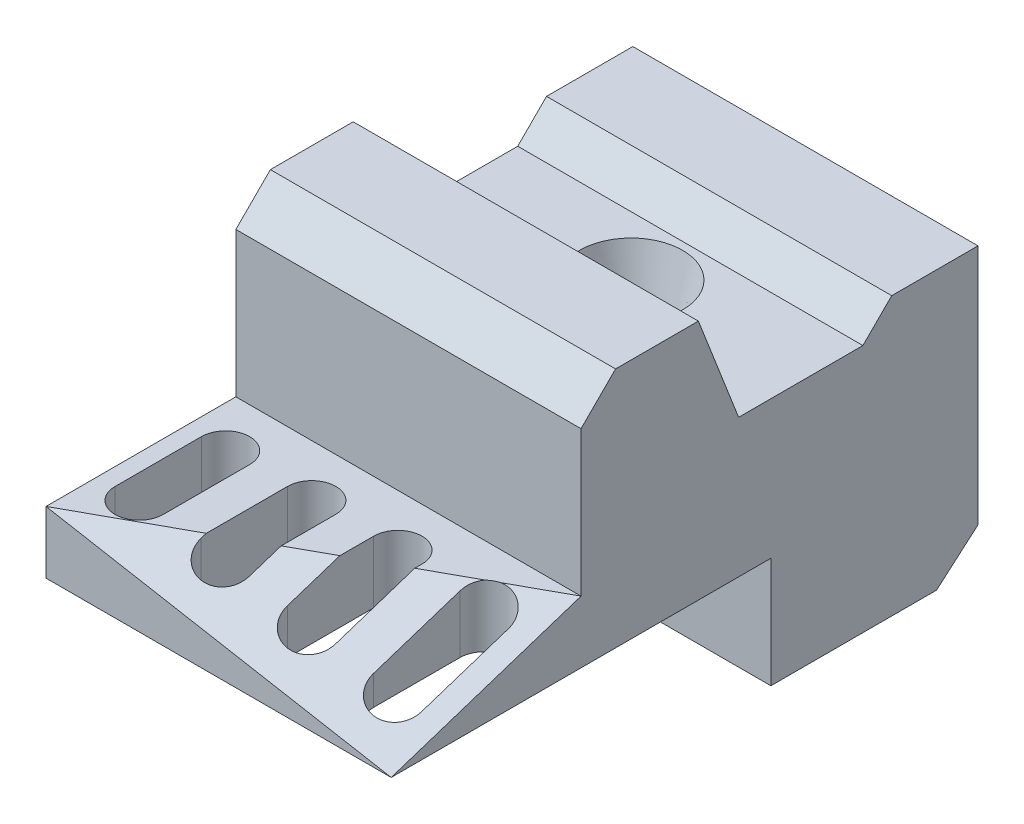
SolidWorks part; units mm, degrees
ref_plane "Plano frontal" through (0, 0, 0) normal (0, 0, 1) x (1, 0, 0)
ref_plane "Plano superior" through (0, 0, 0) normal (0, 1, 0) x (1, 0, 0)
ref_plane "Plano direito" through (0, 0, 0) normal (1, 0, 0) x (0, 0, -1)
sketch "Esboço3" plane through (0, 0, 0) normal (1, 0, 0) x (0, 0, -1)
  line L0 (0, 0) -> (0, -70)
  line L1 (0, 0) -> (-25, 0)
  line L2 (-12, -80.38) -> (-60, -80.38)
  line L3 (-25, 0) -> (-33.3439, -8.3439)
  line L4 (-33.3439, -8.3439) -> (-69.3439, -8.3439)
  line L5 (-60, -80.38) -> (-60, -48.3785)
  line L6 (-69.3439, -8.3439) -> (-81.0015, 21.62)
  line L7 (-81.0015, 21.62) -> (-105.0015, 21.62)
  line L8 (-105.0015, 21.62) -> (-115, 11.6215)
  line L9 (-115, 11.6215) -> (-115, -30.3785)
  line L10 (-115, -30.3785) -> (-170, -30.3785)
  line L11 (-170, -30.3785) -> (-170, -48.3785)
  line L12 (-170, -48.3785) -> (-60, -48.3785)
  line L13 (0, -70) -> (-12, -80.38)
  point P5 (0, -70)
  point P8 (-12, -80.38)
  dimension "D1" = 18
  dimension "D2" = 25
  dimension "D3" = 55
  dimension "D4" = 11.8
  dimension "D5" = 36
  dimension "D6" = 110
  dimension "D7" = 102
  dimension "D8" = 42
  dimension "D9" = 14.14
  dimension "D10" = 24
  dimension "D11" = 80.38
  dimension "D12" = 70
  dimension "D13" = 158
extrude "Ressalto-extrusão1" add sketch "Esboço3" along normal blind 100
sketch "Esboço5" plane through (0, -30.3785, 0) normal (0, 1, 0) x (1, 0, 0)
  line L0 (0, -142.5) -> (100, -142.5) construction
  line L1 (0, -115) -> (0, -170) construction
  line L2 (100, -115) -> (100, -170) construction
  line L3 (12, -155.02) -> (12, -129.98) construction
  line L4 (5, -155.02) -> (5, -129.98)
  line L5 (19, -155.02) -> (19, -129.98)
  line L6 (36.96, -155.02) -> (36.96, -129.98) construction
  line L7 (29.96, -155.02) -> (29.96, -129.98)
  line L8 (43.96, -155.02) -> (43.96, -129.98)
  line L9 (61.92, -155.02) -> (61.92, -129.98) construction
  line L10 (54.92, -155.02) -> (54.92, -129.98)
  line L11 (68.92, -155.02) -> (68.92, -129.98)
  line L12 (86.88, -155.02) -> (86.88, -129.98) construction
  line L13 (79.88, -155.02) -> (79.88, -129.98)
  line L14 (93.88, -155.02) -> (93.88, -129.98)
  line L15 (12, -155.02) -> (36.96, -155.02) construction
  arc A0 (5, -155.02) -> (19, -155.02) centre (12, -155.02) ccw
  arc A1 (19, -129.98) -> (5, -129.98) centre (12, -129.98) ccw
  arc A2 (29.96, -155.02) -> (43.96, -155.02) centre (36.96, -155.02) ccw
  arc A3 (43.96, -129.98) -> (29.96, -129.98) centre (36.96, -129.98) ccw
  arc A4 (54.92, -155.02) -> (68.92, -155.02) centre (61.92, -155.02) ccw
  arc A5 (68.92, -129.98) -> (54.92, -129.98) centre (61.92, -129.98) ccw
  arc A6 (79.88, -155.02) -> (93.88, -155.02) centre (86.88, -155.02) ccw
  arc A7 (93.88, -129.98) -> (79.88, -129.98) centre (86.88, -129.98) ccw
  point P8 (12, -142.5)
  point P16 (36.96, -142.5)
  point P23 (61.92, -142.5)
  point P30 (86.88, -142.5)
  dimension "D1" = 12.52
  dimension "D2" = 7
  dimension "D3" = 5
  dimension "D5" = 24.96
  dimension "D4" = 4
extrude "Corte-extrusão1" cut sketch "Esboço5" against normal through all
ref_plane "Plano1" through (3.9898, 22.1656, 7.2542) normal (0.1686, 0.9368, 0.3066) x (0.9857, -0.1603, -0.0524)
sketch "Esboço6" plane through (3.9898, 22.1656, 7.2542) normal (0.1686, 0.9368, 0.3066) x (0.9857, -0.1603, -0.0524)
  line L0 (-4.0478, -171.0164) -> (97.405, -176.6151)
  line L1 (97.405, -176.6151) -> (97.405, -118.7446)
  line L2 (97.405, -118.7446) -> (-4.0478, -171.0164)
extrude "Corte-extrusão4" cut sketch "Esboço6" along normal blind 87
sketch "Esboço9" plane through (0, 0, 0) normal (-1, 0, 0) x (0, 0, 1)
  line L0 (50, -88.5723) -> (50, 2.8812) construction
  line L1 (60, -48.3785) -> (60, -80.38) construction
  line L2 (-16.2721, -70.38) -> (105.7594, -70.38) construction
  line L3 (60, -80.38) -> (12, -80.38) construction
  line L4 (-17.7282, -41.443) -> (44.833, -95.5585) construction
  line L5 (12, -80.38) -> (0, -70) construction
  line L6 (10, 20.2742) -> (10, -95.5585) construction
  line L7 (0, -70) -> (0, 0) construction
  line L8 (20.4776, -18.3439) -> (99.5877, -18.3439) construction
  line L9 (-11.2225, -10) -> (26.9298, -10) construction
  line L10 (63.9601, 11.62) -> (128.763, 11.62) construction
  line L11 (105, 33.7397) -> (105, -60.5191) construction
  line L12 (67.607, -38.3785) -> (182.0641, -38.3785) construction
  line L13 (0, 0) -> (25, 0) construction
  line L14 (33.3439, -8.3439) -> (69.3439, -8.3439) construction
  line L15 (81.0015, 21.62) -> (105.0015, 21.62) construction
  line L16 (115, 11.6215) -> (115, -30.3785) construction
  line L17 (170, -48.3785) -> (60, -48.3785) construction
  line L18 (-8.6362, 19.4941) -> (39.6153, -28.7574) construction
  line L19 (25, 0) -> (33.3439, -8.3439) construction
  line L20 (95.4379, 31.1462) -> (72.1565, -28.6943) construction
  line L21 (69.3439, -8.3439) -> (81.0015, 21.62) construction
  line L22 (105, 11.62) -> (87.8411, 11.62)
  line L23 (87.8411, 11.62) -> (76.1835, -18.3439)
  line L24 (76.1835, -18.3439) -> (29.7819, -18.3439)
  line L25 (29.7819, -18.3439) -> (21.438, -10)
  line L26 (21.438, -10) -> (10, -10)
  line L27 (10, -10) -> (10, -65.428)
  line L28 (10, -65.428) -> (15.7249, -70.38)
  line L29 (15.7249, -70.38) -> (50, -70.38)
  line L30 (50, -70.38) -> (50, -38.3785)
  line L31 (50, -38.3785) -> (105, -38.3785)
  line L32 (105, -38.3785) -> (105, 11.62)
  dimension "D1" = 10
  dimension "D2" = 10
  dimension "D3" = 10
  dimension "D4" = 10
  dimension "D5" = 10
  dimension "D6" = 10
  dimension "D7" = 10
  dimension "D8" = 10
  dimension "D9" = 10
  dimension "D10" = 10
  dimension "D11" = 10
extrude "Corte-extrusão6" cut sketch "Esboço9" against normal blind 20
sketch "Esboço10" plane through (0, -80.38, 0) normal (0, -1, 0) x (1, 0, 0)
  line L0 (100, 60) -> (0, 60) construction
  circle A0 centre (50, 50.5) radius 9
  point P2 (50, 60)
  dimension "D1" = 9.5
extrude "Corte-extrusão8" cut sketch "Esboço10" against normal up to next
sketch "Esboço12" plane through (0, -8.3439, 0) normal (0, 1, 0) x (1, 0, 0)
  circle A0 centre (50, -50.5) radius 14.94
  point P0 (50, -50.5)
extrude "Corte-extrusão10" cut sketch "Esboço12" against normal blind 24.04 draft 12.85
